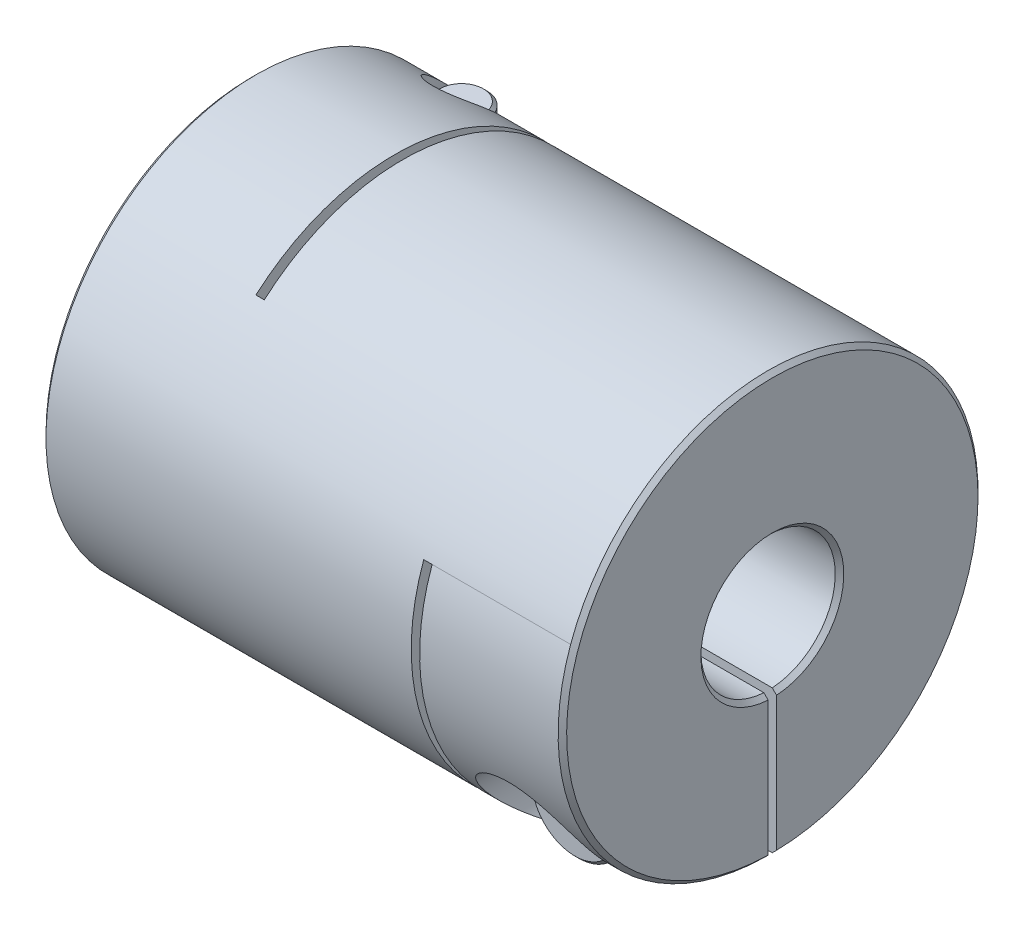
SolidWorks part; units mm, degrees
ref_plane "Front Plane" through (0, 0, 0) normal (0, 0, 1) x (1, 0, 0)
ref_plane "Top Plane" through (0, 0, 0) normal (0, 1, 0) x (1, 0, 0)
ref_plane "Right Plane" through (0, 0, 0) normal (1, 0, 0) x (0, 0, -1)
sketch "Sketch1" plane through (0, 0, 0) normal (1, 0, 0) x (0, 0, -1)
  circle A0 centre (0, 0) radius 12.5
  dimension "dim D" = 25
extrude "Boss-Extrude1" add sketch "Sketch1" along normal mid plane 31
sketch "Sketch2" plane through (15.5, 0, 0) normal (1, 0, 0) x (0, 0, -1)
  circle A0 centre (0, 0) radius 4
  dimension "dim D1" = 8
extrude "Cut-Extrude1" cut sketch "Sketch2" against normal through all
chamfer "Chamfer1" distance 0.254 angle 45 4 edges at (-15.5, 0, -4) (-15.5, 0, -12.5) (15.5, 0, -12.5) (15.5, 0, -4)
ref_plane "Plane2" through (0, -12.5, 0) normal (0, -1, 0) x (1, 0, 0)
ref_plane "L1" through (-11.25, 0, 0) normal (-1, 0, 0) x (0, 0, 1)
sketch "Sketch4" plane through (0, -12.5, 0) normal (0, -1, 0) x (1, 0, 0)
  line L0 (-15.246, -12.5) -> (15.246, -12.5) construction
  line L1 (-7, -12.5) -> (-6.5, -12.5)
  line L2 (-7, -12.5) -> (-7, 8.25)
  line L3 (-7, 8.25) -> (-6.5, 8.25)
  line L4 (-6.5, -12.5) -> (-6.5, 8.25)
  line L5 (-7, 4) -> (-7, 12.5) construction
  line L6 (15.246, 4) -> (-15.246, 4) construction
  line L7 (15.246, 12.5) -> (-15.246, 12.5) construction
  line L10 (-7, 8.25) -> (-15.5, 8.25) construction
  line L11 (-15.5, 12.246) -> (-15.5, -12.246) construction
  line L12 (-11.25, 10.2256) -> (-11.25, -10.2256) construction
  point P16 (-11.25, 8.25)
  dimension "D1" = 0.5
extrude "Cut-Extrude2" cut sketch "Sketch4" against normal through all
ref_plane "Plane4" through (0, 0, -12.5) normal (0, 0, -1) x (-1, 0, 0)
sketch "Sketch7" plane through (0, 0, -12.5) normal (0, 0, -1) x (-1, 0, 0)
  line L1 (-6.5, -12.5) -> (-7, -12.5)
  line L2 (-7, -12.5) -> (-7, 4.25)
  line L3 (-7, 4.25) -> (-6.5, 4.25)
  line L4 (-6.5, -12.5) -> (-6.5, 4.25)
  line L5 (15.5, 8.6487) -> (11.25, 8.6487) construction
  line L7 (-10.505, -12.5) -> (10.505, -12.5) construction
  line L8 (-15.246, -4) -> (6.5, -4) construction
  line L9 (15.5, -12.246) -> (15.5, 12.246) construction
  line L10 (-15.246, -4) -> (6.5, -4) construction
  line L11 (6.5, 9.3908) -> (7, 9.3908) construction
  line L12 (-7, 4.25) -> (-7, -12.5) construction
  line L14 (-15.246, -4) -> (6.5, -4) construction
  line L16 (-15.246, -4) -> (6.5, -4) construction
  line L17 (7, -12.5) -> (15.246, -12.5) construction
  line L18 (11.25, -10.2256) -> (11.25, 10.2256) construction
  line L19 (-15.246, -12.5) -> (-15.246, 12.5) construction
  line L20 (-15.5, 4.25) -> (-11.25, 4.25) construction
  line L21 (-15.5, 12.246) -> (-15.5, -12.246) construction
  line L22 (-11.25, 4.25) -> (-7, 4.25) construction
  line L23 (-15.246, -12.5) -> (-15.246, 12.5) construction
  line L24 (-15.246, -4) -> (-15.246, 12.5) construction
  line L25 (-15.246, -4) -> (6.5, -4) construction
  point P23 (-7, 4.25)
  point P33 (-15.246, 4.25)
extrude "Cut-Extrude3" cut sketch "Sketch7" against normal through all
sketch "Sketch8" plane through (0, 0, 0) normal (0, 1, 0) x (1, 0, 0)
  line L0 (-7, -8.25) -> (-7, 12.5) construction
  line L1 (-15.5, 12.5) -> (-7, 12.5)
  line L2 (-15.5, 12.5) -> (-15.5, 0)
  line L3 (-15.5, 0) -> (-7, 0)
  line L4 (-7, 12.5) -> (-7, 0)
  line L5 (10.505, 12.5) -> (-10.505, 12.5) construction
  line L6 (-15.5, 12.246) -> (-15.5, -12.246) construction
extrude "Cut-Extrude5" cut sketch "Sketch8" against normal mid plane 0.5
sketch "Sketch13" plane through (0, 0, 0) normal (0, 0, 1) x (1, 0, 0)
  line L0 (15.5, -12.246) -> (15.5, 12.246) construction
  line L1 (7, -12.5) -> (15.5, -12.5)
  line L2 (7, -12.5) -> (7, 0)
  line L3 (7, 0) -> (15.5, 0)
  line L4 (15.5, -12.5) -> (15.5, 0)
extrude "Cut-Extrude6" cut sketch "Sketch13" against normal mid plane 0.5
hole_wizard "CBORE for M3 SHCS1" positions "Sketch12" profile "Sketch11" counterbore size "M3" standard "Ansi Metric" end condition through all
sketch "Sketch12" plane through (0, -12.5, 0) normal (0, -1, 0) x (1, 0, 0)
  line L0 (-11.25, 10.2256) -> (-11.25, -10.2256) construction
  line L1 (-7, -3.9922) -> (-7, -12.4975) construction
  line L2 (-7, -3.9922) -> (-7, -12.4975)
  line L3 (-7, -8.2448) -> (-11.25, -8.2448) construction
  point P0 (-11.25, -8.2448)
sketch "Sketch11" plane through (-11.25, -12.5, -8.2448) normal (1, 0, 0) x (0, 0, -1)
  line L0 (0, 0) -> (0, 25)
  line L1 (0, 25) -> (1.7, 25)
  line L3 (1.7, 25) -> (1.7, 8)
  line L4 (1.7, 8) -> (3.25, 8)
  line L5 (3.25, 8) -> (3.25, 0)
  line L7 (3.25, 0) -> (0, 0)
  line L11 (0, -6.35) -> (0, 107.95) construction
  dimension "Thru Hole Dia." = 3.4
  dimension "Thru Hole Depth" = 25
  dimension "C'Bore Dia." = 6.5
  dimension "C'Bore Depth" = 8
ref_plane "Plane5" through (0, 0, 12.5) normal (0, 0, 1) x (1, 0, 0)
hole_wizard "CBORE for M3 SHCS2" positions "Sketch15" profile "Sketch14" counterbore size "M3" standard "Ansi Metric" end condition through all
sketch "Sketch15" plane through (0, 0, 12.5) normal (0, 0, 1) x (1, 0, 0)
  line L0 (-14.5, -4.5) -> (-8, -4.5) construction
  line L1 (-14.5, -4.5) -> (-8, -4.5)
  line L5 (0, 0) -> (0, 12.5) construction
  line L6 (-7, 12.5) -> (-15.246, 12.5) construction
  line L8 (14.5, -4.5) -> (8, -4.5)
  line L9 (11.25, -4.5) -> (11.25, -8.2448) construction
  line L11 (11.25, -12.4975) -> (11.25, -3.9922) construction
  line L12 (15.246, -12.4975) -> (7, -12.4975) construction
  line L13 (7, -3.9922) -> (15.246, -3.9922) construction
  point P0 (11.25, -8.2448)
sketch "Sketch14" plane through (11.25, -8.2448, 12.5) normal (1, 0, 0) x (0, -1, 0)
  line L0 (0, 0) -> (0, 25)
  line L1 (0, 25) -> (1.7, 25)
  line L3 (1.7, 25) -> (1.7, 8)
  line L4 (1.7, 8) -> (3.25, 8)
  line L5 (3.25, 8) -> (3.25, 0)
  line L7 (3.25, 0) -> (0, 0)
  line L11 (0, -6.35) -> (0, 107.95) construction
  dimension "Thru Hole Dia." = 3.4
  dimension "Thru Hole Depth" = 25
  dimension "C'Bore Dia." = 6.5
  dimension "C'Bore Depth" = 8
sketch "Sketch16" plane through (0, 0, 4.5) normal (0, 0, 1) x (1, 0, 0)
  circle A0 centre (11.25, -8.2448) radius 2.75
  dimension "screw dia" = 5.5
extrude "Boss-Extrude2" add sketch "Sketch16" along normal blind 3 separate body
sketch "Sketch17" plane through (0, 0, 4.5) normal (0, 0, -1) x (-1, 0, 0)
  circle A0 centre (-11.25, -8.2448) radius 1.5
  dimension "D1" = 3
extrude "Boss-Extrude3" add sketch "Sketch17" along normal blind 13.5
chamfer "Chamfer2" distance 0.2 angle 45 3 edges at (9.75, -8.2448, -9) (14, -8.2448, 4.5) (14, -8.2448, 7.5)
sketch "Sketch18" plane through (0, 0, 7.5) normal (0, 0, 1) x (1, 0, 0)
  line L1 (11.25, -9.6882) -> (12.5, -8.9665)
  line L2 (12.5, -8.9665) -> (12.5, -7.5232)
  line L3 (12.5, -7.5232) -> (11.25, -6.8015)
  line L4 (11.25, -6.8015) -> (10, -7.5232)
  line L5 (10, -7.5232) -> (10, -8.9665)
  line L6 (10, -8.9665) -> (11.25, -9.6882)
  circle A0 centre (11.25, -8.2448) radius 1.25 construction
  dimension "hex" = 2.5
extrude "Cut-Extrude7" cut sketch "Sketch18" against normal blind 1.5
mirror "Mirror1" about plane through (0, 0, 0) normal (1, 0, 0) of bodies 121
pattern_circular "CirPattern1" count 2 every 90 about axis through (0, 0, 0) along (1, 0, 0) of bodies 122
delete or keep bodies "Body-Delete1" type delete bodies bodies 122
